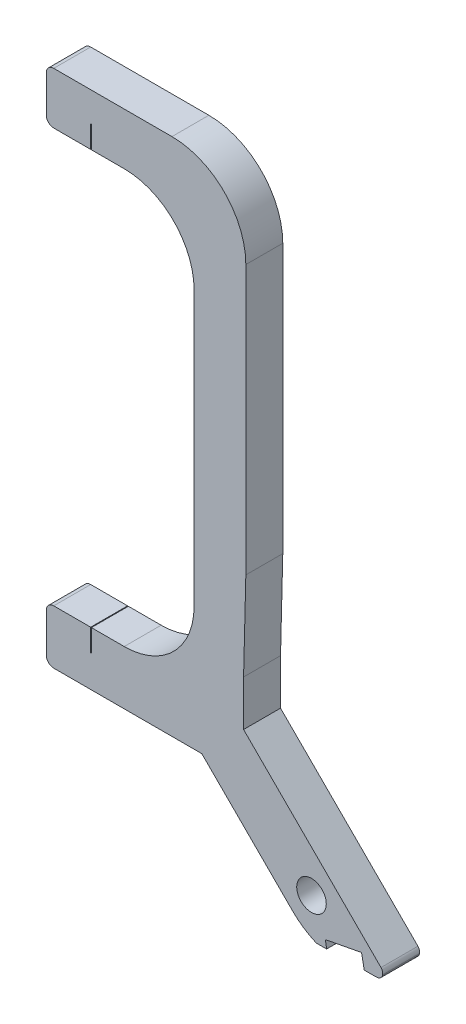
SolidWorks part; units mm, degrees
ref_plane "Front Plane" through (0, 0, 0) normal (0, 0, 1) x (1, 0, 0)
ref_plane "Top Plane" through (0, 0, 0) normal (0, 1, 0) x (1, 0, 0)
ref_plane "Right Plane" through (0, 0, 0) normal (1, 0, 0) x (0, 0, -1)
sketch "Sketch1" plane through (0, 0, 0) normal (0, 0, 1) x (1, 0, 0)
  line L0 (1, 0) -> (17, 0)
  line L1 (27, -10.1647) -> (27, -46.3772)
  line L2 (16.8019, -70.3054) -> (1, -70.3054)
  line L3 (0, -69.3054) -> (0, -64)
  line L4 (1, -63) -> (10.5397, -63)
  line L5 (20, -53.5397) -> (20, -16.4603)
  line L6 (10.5397, -7) -> (1, -7)
  line L7 (0, -6) -> (0, -1)
  line L14 (27, -10.1647) -> (27, -10)
  line L34 (16.8019, -70.3054) -> (26.6946, -70.3054) construction
  line L37 (26.6946, -58.4939) -> (27, -46.3772)
  line L42 (26.6946, -70.3054) -> (26.6946, -58.4939) construction
  line L43 (26.6946, -70.3054) -> (41.8593, -85.47) construction
  line L45 (33.3315, -82.5991) -> (21.0378, -70.3054)
  line L48 (45.2918, -83.2457) -> (26.6946, -64.6485)
  line L49 (37.7477, -85.47) -> (26.6946, -68.5482) construction
  line L50 (24.9375, -70.3054) -> (37.6921, -78.6364) construction
  line L53 (16.8019, -70.3054) -> (21.0378, -70.3054)
  line L54 (26.6946, -58.4939) -> (26.6946, -64.3996)
  line L55 (26.6946, -64.3996) -> (26.6946, -64.6485)
  line L58 (43.4863, -87.0971) -> (46.4915, -90.1022) construction
  line L59 (45.5045, -83.9961) -> (45.4904, -84.0557)
  line L63 (40.9545, -84.5652) -> (41.8968, -84.2994) construction
  line L64 (44.7214, -84.6709) -> (36.7433, -84.7648)
  arc A2 (10.5397, -63) -> (20, -53.5397) centre (10.5397, -53.5397) ccw
  arc A3 (20, -16.4603) -> (10.5397, -7) centre (10.5397, -16.4603) ccw
  arc A4 (0, -64) -> (1, -63) centre (1, -64) cw
  arc A5 (0, -69.3054) -> (1, -70.3054) centre (1, -69.3054) ccw
  arc A6 (0, -1) -> (1, 0) centre (1, -1) cw
  arc A7 (0, -6) -> (1, -7) centre (1, -6) ccw
  arc A8 (17, 0) -> (27, -10) centre (17, -10) cw
  circle A10 centre (35.887, -79.4977) radius 2
  arc A14 (36.4149, -84.6985) -> (33.3315, -82.5991) centre (40.4026, -75.528) cw
  arc A17 (45.4904, -84.0557) -> (44.7214, -84.6709) centre (44.712, -83.871) cw
  arc A18 (45.2918, -83.2457) -> (45.5045, -83.9961) centre (44.7261, -83.8114) cw
  arc A19 (36.4149, -84.6985) -> (36.7433, -84.7648) centre (36.7339, -83.9649) ccw
  point P11 (27, 0)
  point P25 (0, 0)
  point P30 (37.4955, 3.7564)
  point P31 (30.004, -73.6147)
  dimension "D8" = 1
  dimension "D6" = 10
  dimension "D7" = 4
  dimension "D10" = 10
  dimension "D9" = 0.8
  dimension "D11" = 0.8
  dimension "D1" = 7
  dimension "D2" = 7
  dimension "D4" = 20
  dimension "D3" = 135
  dimension "D5" = 13
extrude "Boss-Extrude1" add sketch "Sketch1" along normal blind 5
sketch "Sketch2" plane through (0, -63, 0) normal (0, 1, 0) x (1, 0, 0)
  line L0 (27, -2.5) -> (6.05, -2.5) construction
  line L1 (27, -5) -> (27, 0) construction
  line L2 (10.5397, 0) -> (1, 0) construction
  line L3 (6, -5) -> (6.1, -5)
  line L4 (6, -5) -> (6, 0)
  line L5 (6, 0) -> (6.1, 0)
  line L6 (6.1, -5) -> (6.1, 0)
  line L7 (6, -5) -> (6.1, 0) construction
  line L8 (6, 0) -> (6.1, -5) construction
  dimension "D2" = 0.1
extrude "Cut-Extrude1" cut sketch "Sketch2" against normal blind 3
sketch "Sketch3" plane through (0, -7, 0) normal (0, -1, 0) x (1, 0, 0)
  line L0 (27, 2.5) -> (6.05, 2.5) construction
  line L1 (27, 5) -> (27, 0) construction
  line L2 (1, 5) -> (10.5397, 5) construction
  line L3 (6, 0) -> (6.1, 0)
  line L4 (6, 0) -> (6, 5)
  line L5 (6, 5) -> (6.1, 5)
  line L6 (6.1, 0) -> (6.1, 5)
  line L7 (6, 0) -> (6.1, 5) construction
  line L8 (6, 5) -> (6.1, 0) construction
  dimension "D2" = 0.1
extrude "Cut-Extrude2" cut sketch "Sketch3" against normal blind 3
ref_plane "Plane1" through (17.3154, -90.6979, 0) normal (0.1875, -0.9823, 0) x (0, 0, -1)
sketch "Sketch5" plane through (17.3154, -90.6979, 0) normal (0.1875, -0.9823, 0) x (0, 0, -1)
  line L0 (-2.5, 27.8783) -> (-2.5, 26.3783) construction
  line L1 (-5, 27.8783) -> (0, 27.8783) construction
  line L3 (-5, 21.3783) -> (0, 21.3783)
  line L4 (-5, 21.3783) -> (-5, 26.3783)
  line L5 (-5, 26.3783) -> (0, 26.3783)
  line L6 (0, 21.3783) -> (0, 26.3783)
  line L7 (-5, 21.3783) -> (0, 26.3783) construction
  line L8 (-5, 26.3783) -> (0, 21.3783) construction
  point P4 (-2.5, 23.8783)
  dimension "D1" = 1.5
  dimension "D2" = 5
extrude "Cut-Extrude3" cut sketch "Sketch5" against normal blind 3
equation "\"A.L\"= 0.07m"
equation "\"A.h\"= 0.007m"
equation "\"A.d\"= 0.005m"
equation "\"A.delta\"= 45.0001"
equation "\"A.w\"= 0m"
equation "\"A.v\"= 0.013m"
equation "\"A.s\"= 0.014m"
equation "\"A.t\"= 0.007m"
equation "\"B.L\"= 0.065m"
equation "\"B.h\"= 0.008m"
equation "\"B.s\"= 0.016m"
equation "\"B.t\"= 0.008m"
equation "\"C.h\"= 0.0065m"
equation "\"C.d\"= 0.005m"
equation "\"C.L\"= 0.05m"
equation "\"C.wmax\"= 0.003m"
equation "\"D.L\"= 0.06m"
equation "\"D.h\"= 0.008m"
equation "\"D.s\"= 0.012m"
equation "\"D.t\"= 0.008m"
equation "\"a_h\"= 0.0001m"
equation "\"a_d\"= 0.005m"
equation "\"a_L\"= 0.008m"
equation "\"b_h\"= 0.0004m"
equation "\"b_d\"= 0.005m"
equation "\"b_L\"= 0.007m"
equation "\"c_h\"= 0.0001m"
equation "\"c_d\"= 0.005m"
equation "\"c_L\"= 0.01m"
equation "\"d_h\"= 0.0001m"
equation "\"d_d\"= 0.005m"
equation "\"d_L\"= 0.01m"
equation "\"S.h\"= 0.015m"
equation "\"S.L\"= 0.09275m"
equation "\"D1@Sketch1\"=\"A.h\""
equation "\"D2@Sketch1\"=\"A.t\""
equation "\"D4@Sketch1\"=\"A.s\"+0.006"
equation "\"D1@Boss-Extrude1\"=\"A.d\""
equation "\"D1@Sketch2\"=\"A.h\"+\"A.s\"-\"a_h\"/2"
equation "\"D2@Sketch2\"=\"d_h\""
equation "\"D1@Sketch3\"=\"A.h\"+\"A.s\"-\"d_h\"/2"
equation "\"D2@Sketch3\"=\"d_h\""
equation "\"D5@Sketch1\"=0.013m"
